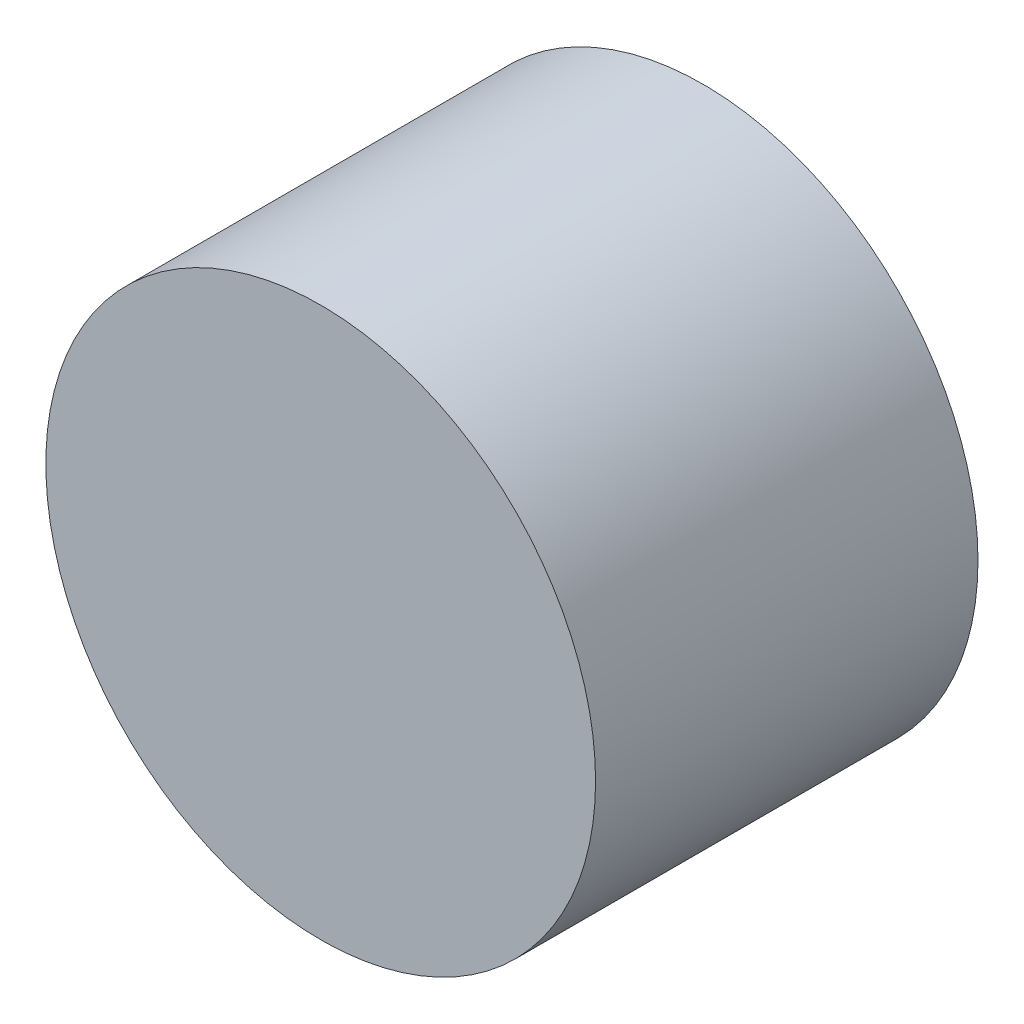
SolidWorks part; units mm, degrees
ref_plane "Front Plane" through (0, 0, 0) normal (0, 0, 1) x (1, 0, 0)
ref_plane "Top Plane" through (0, 0, 0) normal (0, 1, 0) x (1, 0, 0)
ref_plane "Right Plane" through (0, 0, 0) normal (1, 0, 0) x (0, 0, -1)
sketch "Sketch1" plane through (0, 0, 0) normal (0, 0, 1) x (1, 0, 0)
  circle A0 centre (0, 0) radius 18.2562
  dimension "D1" = 36.5125
extrude "Boss-Extrude1" add sketch "Sketch1" along normal blind 25.4
sketch "Sketch2" plane through (0, 0, 25.4) normal (0, 0, 1) x (1, 0, 0)
  circle A0 centre (0, 0) radius 6.35
  circle A1 centre (0, 0) radius 18.2562
  circle A2 centre (0, 0) radius 18.2562
  dimension "D2" = 12.7
  dimension "D1" = 0
